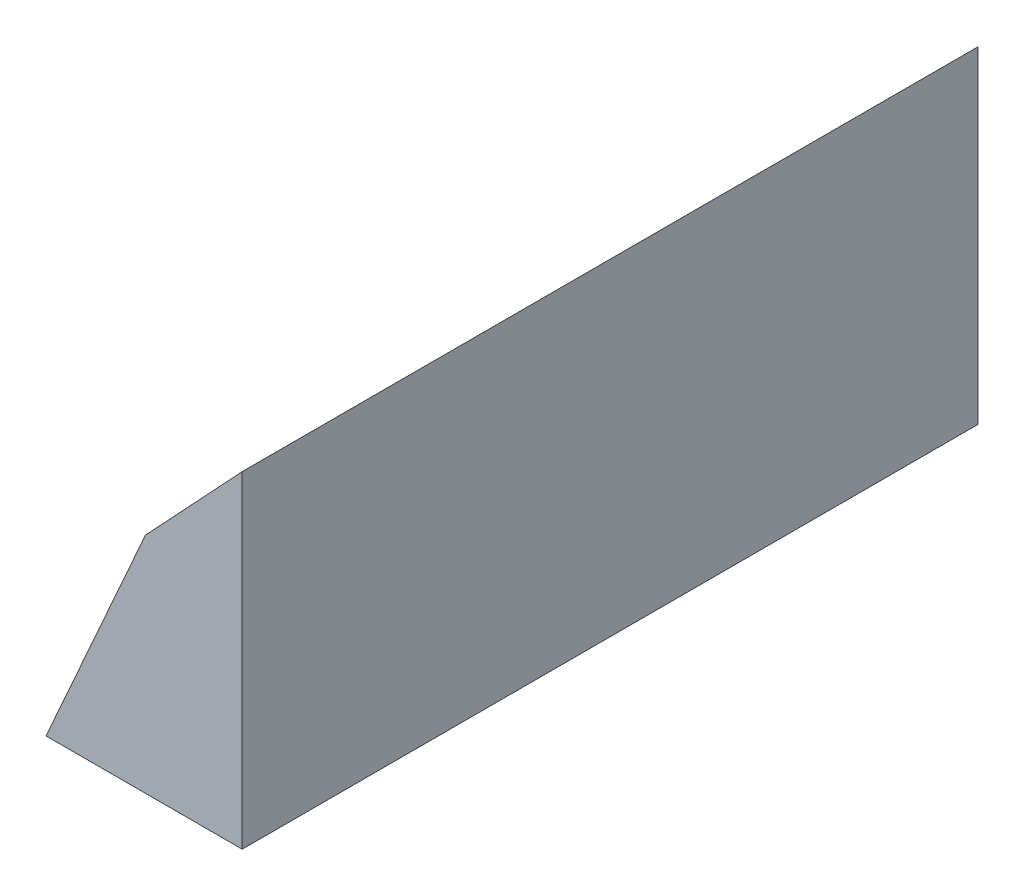
SolidWorks part; units mm, degrees
ref_plane "Front Plane" through (0, 0, 0) normal (0, 0, 1) x (1, 0, 0)
ref_plane "Top Plane" through (0, 0, 0) normal (0, 1, 0) x (1, 0, 0)
ref_plane "Right Plane" through (0, 0, 0) normal (1, 0, 0) x (0, 0, -1)
sketch "Sketch1" plane through (0, 0, 0) normal (0, 0, 1) x (1, 0, 0)
  line L0 (-60, -52.5943) -> (0, -52.5943)
  line L1 (0, -52.5943) -> (0, 47.4057)
  line L3 (-60, -52.5943) -> (-29.5867, 15.7965)
  line L4 (-29.5867, 15.7965) -> (0, 47.4057)
  point P2 (-20.6324, 25.5774)
  point P6 (-19.117, 31.9143)
  point P7 (-29.5867, 15.7965)
  dimension "D1" = 100
  dimension "D2" = 60
extrude "Boss-Extrude1" add sketch "Sketch1" along normal blind 225
sketch "Sketch2" plane through (0, -52.5943, 0) normal (0, -1, 0) x (1, 0, 0)
  line L0 (-60, 225) -> (0, 225) construction
  line L1 (-60, 0) -> (0, 0) construction
  circle A0 centre (-30, 202.5) radius 4.5
  circle A1 centre (-30, 22.5) radius 4.5
  dimension "D1" = 22.5
  dimension "D2" = 22.5
extrude "Cut-Extrude5" cut sketch "Sketch2" against normal through all
ref_plane "Plane1" through (0, -49.5943, 0) normal (0, -1, 0) x (-1, 0, 0)
sketch "Sketch6" plane through (0, -49.5943, 0) normal (0, -1, 0) x (-1, 0, 0)
  circle A0 centre (30, -22.5) radius 8
  circle A1 centre (30, -202.5) radius 8
extrude "Cut-Extrude6" cut sketch "Sketch6" against normal through all
